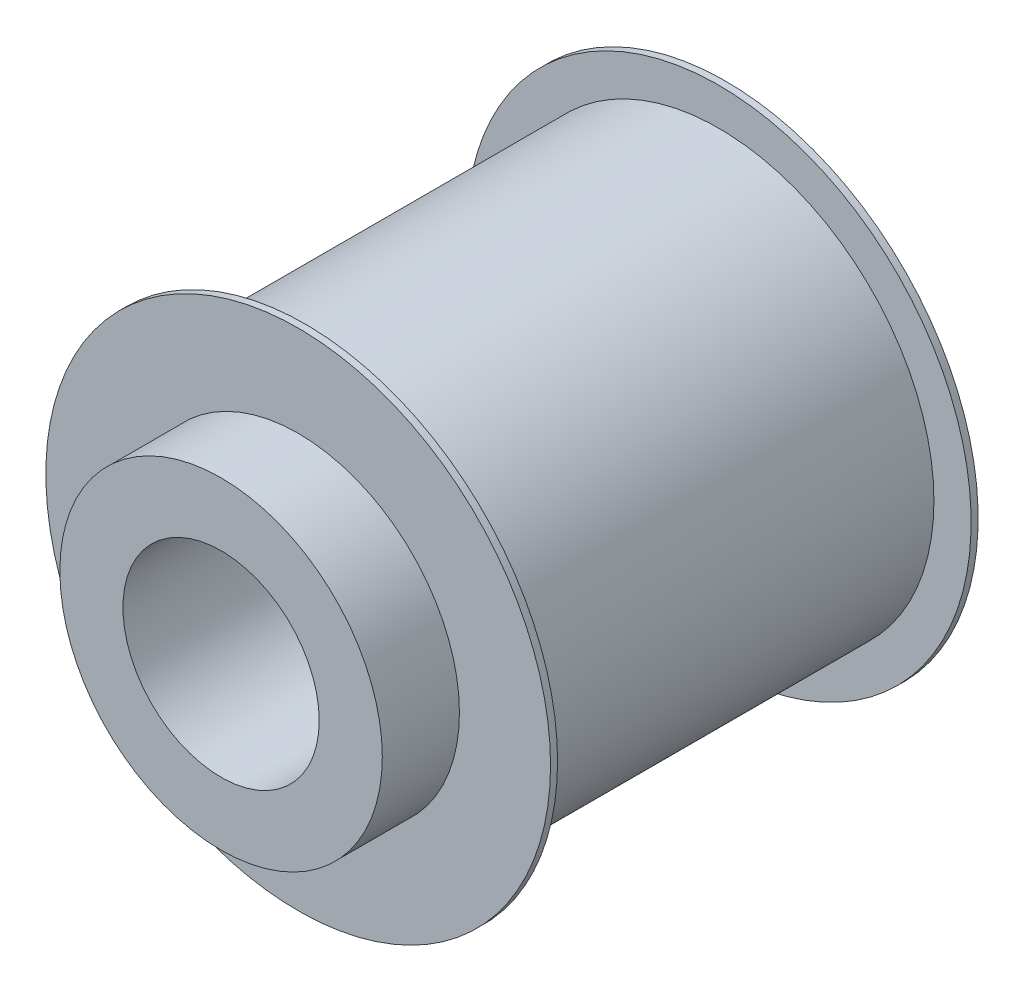
SolidWorks part; units mm, degrees
ref_plane "Płaszczyzna przednia" through (0, 0, 0) normal (0, 0, 1) x (1, 0, 0)
ref_plane "Płaszczyzna górna" through (0, 0, 0) normal (0, 1, 0) x (1, 0, 0)
ref_plane "Płaszczyzna prawa" through (0, 0, 0) normal (1, 0, 0) x (0, 0, -1)
sketch "Szkic1" plane through (0, 0, 0) normal (0, 0, 1) x (1, 0, 0)
  circle A0 centre (0, 0) radius 15.345
  dimension "D1" = 30.69
extrude "Dodanie-wyciągnięcie1" add sketch "Szkic1" along normal blind 30.5
sketch "Szkic2" plane through (0, 0, 30.5) normal (0, 0, 1) x (1, 0, 0)
  circle A0 centre (0, 0) radius 11.5
  dimension "D1" = 23
extrude "Dodanie-wyciągnięcie2" add sketch "Szkic2" along normal blind 5.5
sketch "Szkic3" plane through (0, 0, 30.5) normal (0, 0, 1) x (1, 0, 0)
  circle A0 centre (0, 0) radius 18
  dimension "D1" = 36
extrude "Dodanie-wyciągnięcie3" add sketch "Szkic3" against normal blind 0.5
sketch "Szkic9" plane through (0, 0, 0) normal (0, 0, -1) x (-1, 0, 0)
  circle A0 centre (0, 0) radius 18
  dimension "D1" = 36
extrude "Dodanie-wyciągnięcie6" add sketch "Szkic9" against normal blind 0.5
sketch "Szkic6" plane through (0, 0, 36) normal (0, 0, 1) x (1, 0, 0)
  circle A0 centre (0, 0) radius 7
  dimension "D1" = 14
extrude "Wytnij-wyciągnięcie1" cut sketch "Szkic6" against normal through all
sketch "Szkic7" plane through (0, 0, 36) normal (0, 0, 1) x (1, 0, 0)
  line L1 (-3.5913, 7) -> (3.5688, 7)
  line L2 (-3.5913, 7) -> (-3.5913, 6)
  line L3 (-3.5913, 6) -> (3.5688, 6)
  line L4 (3.5688, 7) -> (3.5688, 6)
  circle A0 centre (0, 0) radius 7 construction
  dimension "D1" = 1
extrude "Dodanie-wyciągnięcie4" [suppressed] add sketch "Szkic7" against normal blind 26
